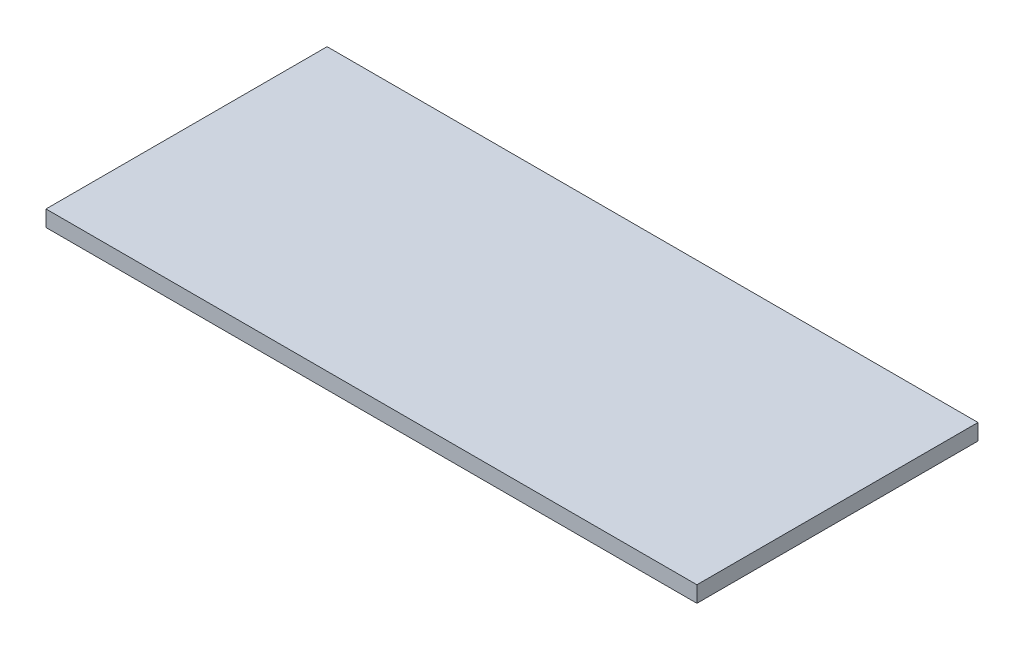
SolidWorks part; units mm, degrees
ref_plane "Front Plane" through (0, 0, 0) normal (0, 0, 1) x (1, 0, 0)
ref_plane "Top Plane" through (0, 0, 0) normal (0, 1, 0) x (1, 0, 0)
ref_plane "Right Plane" through (0, 0, 0) normal (1, 0, 0) x (0, 0, -1)
sketch "Sketch1" plane through (0, 0, 0) normal (0, 1, 0) x (1, 0, 0)
  line L0 (-1140, -620) -> (1731.39, 620) construction
  line L1 (-1140, -620) -> (1140, -620)
  line L2 (-1140, -620) -> (-1140, 620)
  line L3 (-1140, 620) -> (1140, 620)
  line L5 (1731.39, -620) -> (-1140, 620) construction
  line L7 (1489.0685, -282.3858) -> (-897.6785, -282.3858)
  line L8 (1140, -620) -> (1731.39, -620)
  line L13 (1731.39, -620) -> (1731.39, 620)
  line L14 (1731.39, 620) -> (1140, 620)
  line L15 (1489.0685, -282.3858) -> (1489.0685, 282.3858)
  line L16 (1489.0685, 282.3858) -> (-897.6785, 282.3858)
  line L17 (-897.6785, -282.3858) -> (-897.6785, 282.3858)
  line L18 (1489.0685, -282.3858) -> (-897.6785, 282.3858) construction
  line L19 (1489.0685, 282.3858) -> (-897.6785, -282.3858) construction
  point P0 (0, 0)
  point P6 (295.695, 0)
  point P9 (0, 0)
  point P12 (0, 282.3858)
  dimension "D1" = 2280
  dimension "D2" = 1240
extrude "Boss-Extrude1" add sketch "Sketch1" against normal blind 71 contours L17 L7 L15 L16 | L13 L14 L3 L2 L1 L8 L7 L17 L16 L15
